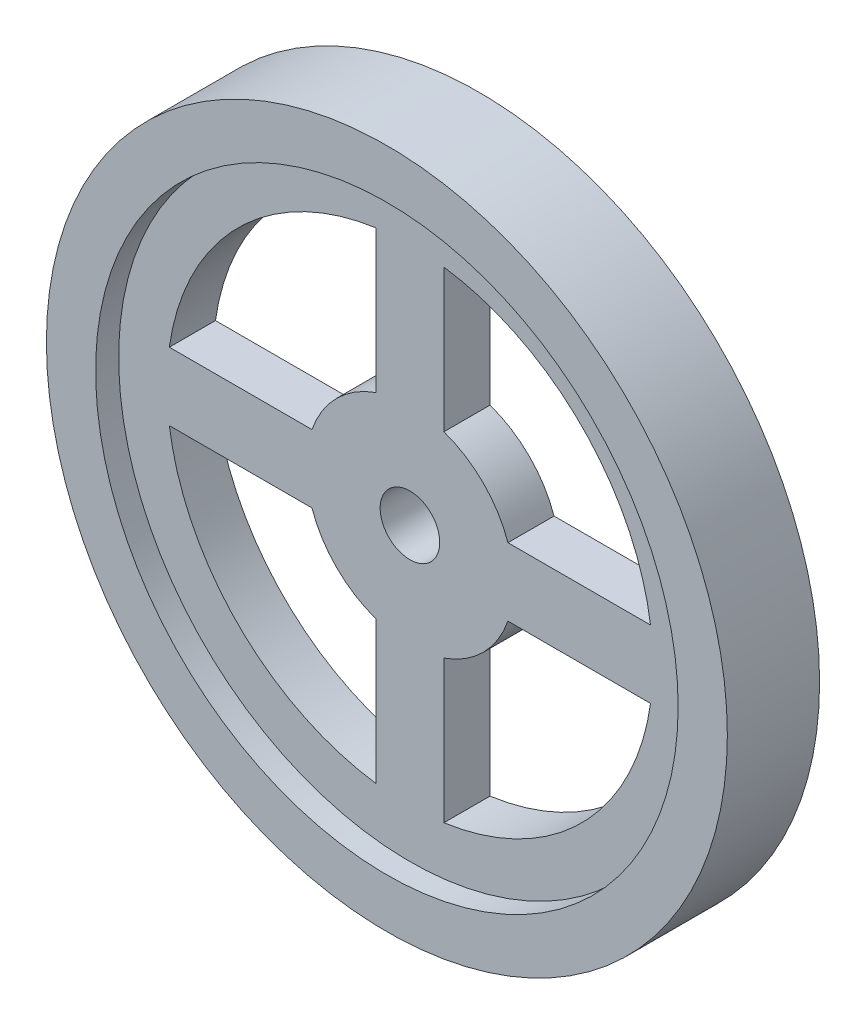
SolidWorks part; units mm, degrees
ref_plane "Front Plane" through (0, 0, 0) normal (0, 0, 1) x (1, 0, 0)
ref_plane "Top Plane" through (0, 0, 0) normal (0, 1, 0) x (1, 0, 0)
ref_plane "Right Plane" through (0, 0, 0) normal (1, 0, 0) x (0, 0, -1)
sketch "Sketch1" plane through (0, 0, 0) normal (0, 0, 1) x (1, 0, 0)
  circle A0 centre (0, 0) radius 37.5
  dimension "D1" = 75
extrude "Boss-Extrude1" add sketch "Sketch1" along normal blind 10.16
sketch "Sketch2" plane through (0, 0, 10.16) normal (0, 0, 1) x (1, 0, 0)
  circle A0 centre (0, 0) radius 32.0812
extrude "Cut-Extrude1" cut sketch "Sketch2" against normal blind 10.16
ref_plane "Plane1" through (0, 0, 5.08) normal (0, 0, 1) x (1, 0, 0)
sketch "Sketch4" plane through (0, 0, 5.08) normal (0, 0, 1) x (1, 0, 0)
  circle A0 centre (0, 0) radius 32.0812
extrude "Boss-Extrude3" add sketch "Sketch4" along normal blind 2.54 and the other way blind 2.54
sketch "Sketch5" plane through (0, 0, 7.62) normal (0, 0, 1) x (1, 0, 0)
  line L0 (-3.7389, 10.7919) -> (-3.7389, 26.5003)
  line L1 (3.7389, 10.7919) -> (3.7389, 26.5003)
  line L2 (10.7919, 3.7389) -> (26.5003, 3.7389)
  line L3 (10.7919, -3.7389) -> (26.5003, -3.7389)
  line L4 (3.7389, -10.7919) -> (3.7389, -26.5003)
  line L5 (-3.7389, -10.7919) -> (-3.7389, -26.5003)
  line L6 (-10.7919, -3.7389) -> (-26.5003, -3.7389)
  line L7 (-10.7919, 3.7389) -> (-26.5003, 3.7389)
  arc A0 (-3.7389, 26.5003) -> (-26.5003, 3.7389) centre (0, 0) ccw
  arc A1 (-10.7919, -3.7389) -> (-3.7389, -10.7919) centre (0, 0) ccw
  arc A2 (3.7389, -26.5003) -> (26.5003, -3.7389) centre (0, 0) ccw
  arc A3 (-26.5003, -3.7389) -> (-3.7389, -26.5003) centre (0, 0) ccw
  arc A4 (26.5003, 3.7389) -> (3.7389, 26.5003) centre (0, 0) ccw
  arc A5 (-3.7389, 10.7919) -> (-10.7919, 3.7389) centre (0, 0) ccw
  arc A6 (10.7919, 3.7389) -> (3.7389, 10.7919) centre (0, 0) ccw
  arc A7 (3.7389, -10.7919) -> (10.7919, -3.7389) centre (0, 0) ccw
  point P23 (0, 0)
  dimension "D1" = 4
extrude "Cut-Extrude2" cut sketch "Sketch5" against normal blind 15.24
sketch "Sketch6" plane through (0, 0, 7.62) normal (0, 0, 1) x (1, 0, 0)
  circle A0 centre (0, 0) radius 3.2811
extrude "Cut-Extrude3" cut sketch "Sketch6" against normal blind 15.24
